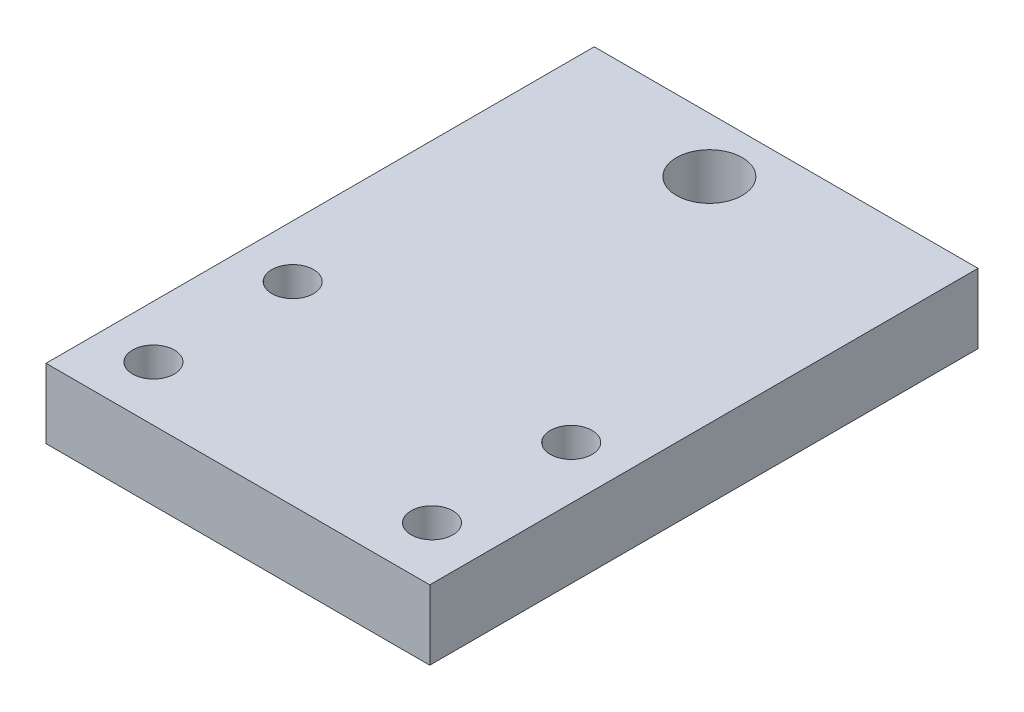
SolidWorks part; units mm, degrees
ref_plane "Front Plane" through (0, 0, 0) normal (0, 0, 1) x (1, 0, 0)
ref_plane "Top Plane" through (0, 0, 0) normal (0, 1, 0) x (1, 0, 0)
ref_plane "Right Plane" through (0, 0, 0) normal (1, 0, 0) x (0, 0, -1)
sketch "Sketch1" plane through (0, 0, 0) normal (0, 1, 0) x (1, 0, 0)
  line L0 (17.5, 50) -> (17.5, 0) construction
  line L1 (0, 50) -> (35, 50)
  line L2 (0, 50) -> (0, 0)
  line L3 (0, 0) -> (35, 0)
  line L4 (35, 50) -> (35, 0)
  line L5 (4.8, 5) -> (30.2, 5) construction
  line L6 (15.5, 5) -> (15.5, 45)
  circle A0 centre (15.5, 45) radius 3
  circle A1 centre (4.8, 5) radius 1.905
  circle A2 centre (30.2, 5) radius 1.905
  circle A3 centre (4.8, 17.7) radius 1.905
  circle A4 centre (30.2, 17.7) radius 1.905
  point P11 (17.5, 50)
  point P13 (17.5, 0)
  point P18 (0, 0)
  point P19 (17.5, 5)
  point P20 (0, 0)
  point P23 (0, 0)
  point P25 (17.5, 25)
  point P26 (15.5, 25)
  dimension "D4" = 6
  dimension "D6" = 3.81
  dimension "D1" = 50
  dimension "D2" = 35
  dimension "D3" = 2
  dimension "D5" = 25.4
  dimension "D7" = 40
  dimension "D8" = 12.7
extrude "Boss-Extrude1" add sketch "Sketch1" along normal blind 6.35
